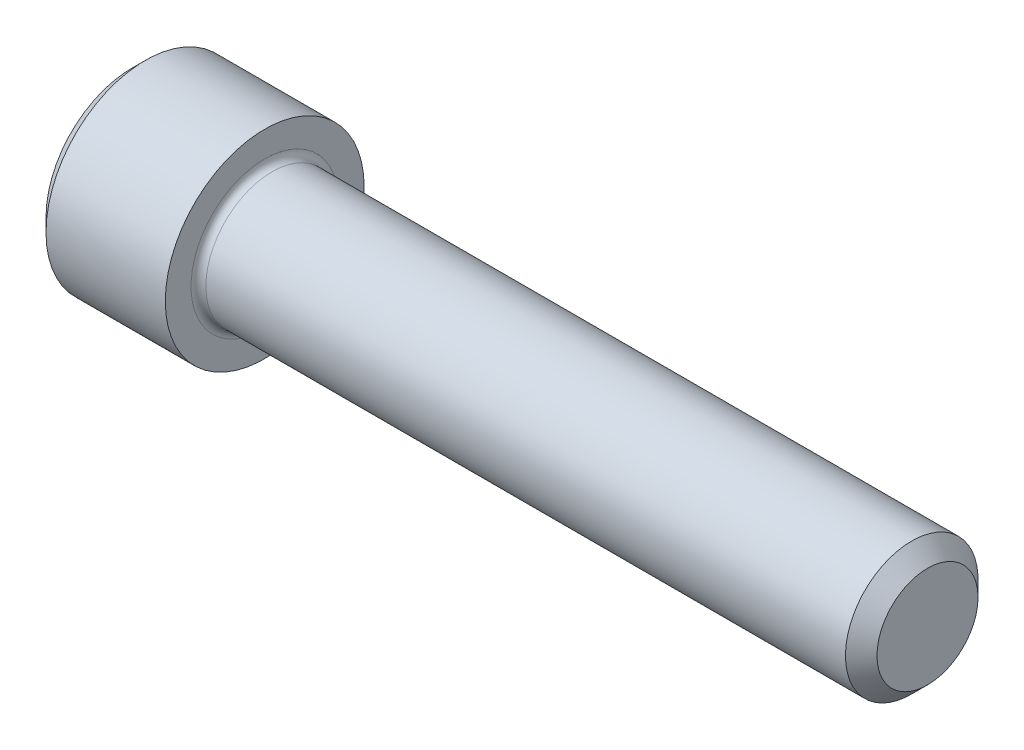
SolidWorks part; units mm, degrees
revolve "Base-Revolve" add sketch "BodySke"
sketch "BodySke" plane through (0, 0, 0) normal (0, 0, 1) x (1, 0, 0)
  line L0 (0, 0) -> (0, 4.1275)
  line L1 (0.635, 4.7625) -> (6.35, 4.7625)
  line L2 (6.35, 4.7625) -> (6.35, 3.175)
  line L3 (6.35, 3.175) -> (37.3444, 3.175)
  line L4 (38.1, 2.4193) -> (38.1, 0)
  line L5 (38.1, 0) -> (0, 0)
  line L6 (-31.75, 0) -> (127, 0) construction
  line L7 (0, 4.1275) -> (0.635, 4.7625)
  line L8 (38.1, 2.4193) -> (37.3444, 3.175)
  line L9 (0, -4.1275) -> (0.635, -4.7625) construction
  line L10 (38.1, -2.4193) -> (37.3444, -3.175) construction
  line L11 (7.62, 9.525) -> (7.62, 3.175) construction
  line L12 (6.35, 9.525) -> (6.35, 3.175) construction
  line L13 (0, 9.525) -> (0, 3.175) construction
  dimension "Diameter" = 6.35
  dimension "Head_ht" = 6.35
  dimension "Length" = 31.75
  dimension "Body_ch_ang" = 45
  dimension "Head_dia" = 9.525
  dimension "Head_ch_ang" = 45
  dimension "Head_side_ht" = 5.715
  dimension "Minor_dia" = 4.8387
  dimension "Advance" = 1.27
  dimension "Thread_nom" = 31.75
  dimension "Thread_length" = 38.1
cosmetic thread "ThreadCosmetic" [suppressed]
fillet "Fillet1" radius 0.3556 1 edges at (6.35, 0, 3.175)
ref_plane "Plane1" through (0, 0, 0) normal (0, 0, 1) x (1, 0, 0)
ref_plane "Plane2" through (0, 0, 0) normal (0, 1, 0) x (1, 0, 0)
ref_plane "Plane3" through (0, 0, 0) normal (1, 0, 0) x (0, 0, -1)
sketch "Sketch2" plane through (0, 0, 0) normal (0, 0, 1) x (1, 0, 0)
  line L0 (0, 2.3813) -> (3.048, 2.3812)
  line L1 (3.048, 2.3812) -> (4.4228, 0)
  line L2 (-31.75, 0) -> (127, 0) construction
  line L3 (4.4228, 0) -> (0, 0)
  line L4 (0, 0) -> (0, 2.3813)
  line L5 (0, 4.1275) -> (0, -4.1275) construction
  line L6 (0, 0) -> (47.625, 0) construction
  line L7 (6.35, -4.7625) -> (6.35, 4.7625) construction
  dimension "D1" = 2.3813
  dimension "D2" = 60
revolve "Hex-PreBroach" cut sketch "Sketch2" angle 360 about L6
sketch "Sketch3" plane through (0, 0, 0) normal (-1, 0, 0) x (0, 0.5, 0.866)
  line L0 (1.3748, 2.3813) -> (-1.3748, 2.3813)
  line L1 (-1.3748, 2.3813) -> (-2.7496, 0)
  line L2 (1.3748, 2.3813) -> (2.7496, 0)
  line L3 (1.3748, -2.3812) -> (2.7496, 0)
  line L4 (1.3748, -2.3812) -> (-1.3748, -2.3812)
  line L5 (-1.3748, -2.3812) -> (-2.7496, 0)
  dimension "D1" = 2.3813
  dimension "D2" = 2.3813
  dimension "Hex_size" = 4.7625
extrude "Hex" cut sketch "Sketch3" against normal blind 3.048
sketch "Sketch4" plane through (0, 0, 0) normal (-1, 0, 0) x (0, 0, 1)
  line L0 (0, 0) -> (2.8067, 0)
  line L1 (0, 0) -> (6.1484, 3.5498) construction
  line L2 (0, 0) -> (1.4033, 2.4307)
  line L3 (2.3336, 0.614) -> (2.6851, 0.817)
  line L4 (1.6986, 1.7139) -> (2.0501, 1.9169)
  arc A0 (2.3336, 0.614) -> (1.6986, 1.7139) centre (0, 0) ccw
  arc A1 (2.8067, 0) -> (2.6851, 0.817) centre (0, 0) ccw
  arc A2 (1.4033, 2.4307) -> (2.0501, 1.9169) centre (0, 0) cw
  dimension "D1" = 30
  dimension "D2" = 60
  dimension "Spline_p_dim" = 1.27
  dimension "D3" = 0.635
extrude "Spline" [suppressed] cut sketch "Sketch4" against normal blind 3.048
pattern_circular "CirPattern1" [suppressed] count 6 every 60
sketch "Sketch5" plane through (0, 0, 0) normal (0, 0, 1) x (1, 0, 0)
  line L0 (-31.75, 0) -> (127, 0) construction
  line L2 (0, 4.1275) -> (0, -4.1275) construction
  circle A0 centre (2.159, 0) radius 0.5905
  dimension "Drilled_hole_dia" = 1.1811
  dimension "Drilled_hole_loc" = 2.159
extrude "Hole" [suppressed] cut sketch "Sketch5" against normal through all and the other way through all
pattern_circular "Drilled-4" [suppressed] count 2 every 60
pattern_circular "Drilled-6" [suppressed] count 3 every 60
sketch "ThdSchSke" plane through (0, 0, 0) normal (0, 0, 1) x (1, 0, 0)
  line L0 (7.62, -2.4194) -> (7.0909, -3.175)
  line L1 (7.62, -2.4194) -> (8.1491, -3.175)
  line L2 (8.1491, -3.175) -> (8.1491, -3.9688)
  line L3 (-3.175, 0) -> (5.1513, 0) construction
  line L5 (8.1491, -3.9688) -> (7.0909, -3.9688)
  line L6 (7.0909, -3.9688) -> (7.0909, -3.175)
  line L7 (0, 4.1275) -> (0, -4.1275) construction
  dimension "Thread_minor" = 4.8387
  dimension "Diameter" = 6.35
  dimension "Start" = 7.62
revolve "ThreadSchematic" [suppressed] cut sketch "ThdSchSke" angle 360 about L3
pattern_linear "ThdSchPat" [suppressed]
equation "\"D2@Sketch3\" = \"Hex_size@Sketch3\" / 2"
equation "\"D1@Sketch3\" = \"Hex_size@Sketch3\" / 2"
equation "\"D1@Sketch2\" = \"Hex_size@Sketch3\" / 2"
equation "\"D3@Sketch4\" = \"Spline_p_dim@Sketch4\" / 2"
equation "\"Thread_minor@ThreadCosmetic\"  =  \"Minor_dia@BodySke\""
equation "\"D2@CirPattern1\" = 360 / \"Num_teeth@CirPattern1\""
equation "\"Wall_thickness@Sketch2\" = \"Head_ht@BodySke\" - \"Key_eng@Hex\""
equation "\"Thread_length@ThreadCosmetic\" = ((sgn( (\"Length@BodySke\" - \"Advance@BodySke\" ) - \"Thread_nom@BodySke\" )-1)*( (\"Length@BodySke\" - \"Advance@BodySke\" ) - \"Thread_nom@BodySke\" ))/-2+ \"Thread_nom@BodySke\""
equation "\"Thread_minor@ThdSchSke\" = \"Minor_dia@BodySke\""
equation "\"Diameter@ThdSchSke\" = \"Diameter@BodySke\""
equation "\"Overcut@ThdSchSke\" = \"Diameter@BodySke\" * 1.25"
equation "\"Start@ThdSchSke\" = \"Head_ht@BodySke\" + \"Length@BodySke\" - \"Thread_length@ThreadCosmetic\"  '---Non-countersunk---"
equation "\"Num_threads@ThdSchPat\" = int( \"Thread_length@ThreadCosmetic\" / \"Advance@BodySke\" + 0.999 )  + 1"
equation "\"Advance@ThdSchPat\" = \"Thread_length@ThreadCosmetic\" /  (\"Num_threads@ThdSchPat\" - 1) 'relax it"
equation "\"Num_threads@ThdSchPat\" = \"Num_threads@ThdSchPat\" - sgn( \"Num_threads@ThdSchPat\" - 1) '---chamfered tips only---"
